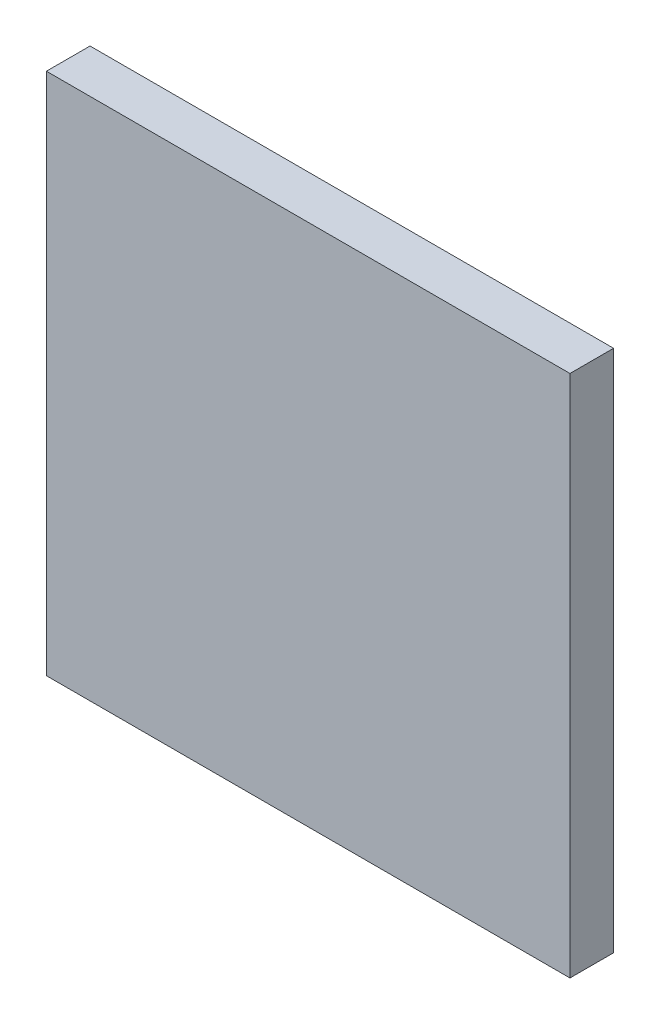
SolidWorks part; units mm, degrees
material "PVC 0.007 Plasticized"
ref_plane "Front Plane" through (0, 0, 0) normal (0, 0, 1) x (1, 0, 0)
ref_plane "Top Plane" through (0, 0, 0) normal (0, 1, 0) x (1, 0, 0)
ref_plane "Right Plane" through (0, 0, 0) normal (1, 0, 0) x (0, 0, -1)
sketch "Sketch1" plane through (0, 0, 0) normal (1, 0, 0) x (0, 0, -1)
  line L1 (-3.175, -38.1) -> (3.175, -38.1)
  line L2 (-3.175, -38.1) -> (-3.175, 38.1)
  line L3 (-3.175, 38.1) -> (3.175, 38.1)
  line L4 (3.175, -38.1) -> (3.175, 38.1)
  line L5 (-3.175, -38.1) -> (3.175, 38.1) construction
  line L6 (-3.175, 38.1) -> (3.175, -38.1) construction
  point P0 (0, 0)
  dimension "D1" = 76.2
  dimension "D2" = 6.35
extrude "Boss-Extrude1" add sketch "Sketch1" along normal blind 76.2
equation "\"D2@Sketch1\"=1in/4"
equation "\"D1@Boss-Extrude1\"=3in"
